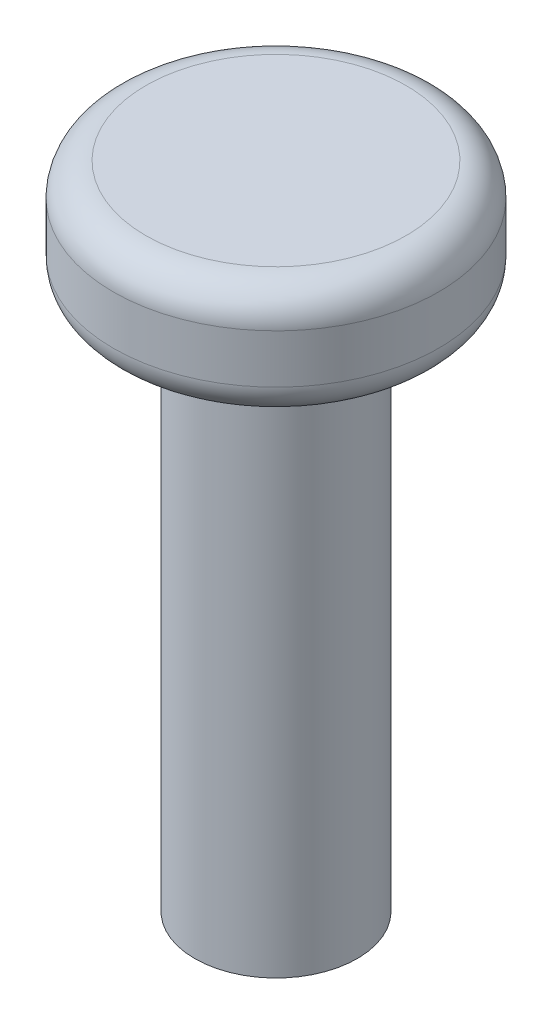
SolidWorks part; units mm, degrees
ref_plane "Front Plane" through (0, 0, 0) normal (0, 0, 1) x (1, 0, 0)
ref_plane "Top Plane" through (0, 0, 0) normal (0, 1, 0) x (1, 0, 0)
ref_plane "Right Plane" through (0, 0, 0) normal (1, 0, 0) x (0, 0, -1)
sketch "Sketch2" plane through (0, 0, 0) normal (0, 1, 0) x (1, 0, 0)
  line L1 (-1, 0.625) -> (1, 0.625)
  line L2 (-1, 0.625) -> (-1, -0.625)
  line L3 (-1, -0.625) -> (1, -0.625)
  line L4 (1, 0.625) -> (1, -0.625)
  line L5 (-1, 0.625) -> (1, -0.625) construction
  line L6 (-1, -0.625) -> (1, 0.625) construction
  circle A0 centre (0, 0) radius 2.5
  dimension "D1" = 5
  dimension "D2" = 1.25
  dimension "D3" = 2
extrude "Boss-Extrude1" add sketch "Sketch2" along normal mid plane 20
fillet "Fillet1" radius 1 1 edges at (0, 10, 2.5)
sketch "Sketch3" plane through (0, 10, 0) normal (0, 1, 0) x (1, 0, 0)
  line L0 (1, -0.625) -> (1, 0.625) construction
  line L1 (-1, -0.625) -> (1, -0.625) construction
  line L2 (-1, 0.625) -> (-1, -0.625) construction
  line L3 (1, 0.625) -> (-1, 0.625) construction
  line L4 (1, -0.625) -> (1, 0.625)
  line L5 (-1, -0.625) -> (1, -0.625)
  line L6 (-1, 0.625) -> (-1, -0.625)
  line L7 (1, 0.625) -> (-1, 0.625)
extrude "Boss-Extrude5" add sketch "Sketch3" against normal blind 16
sketch "Sketch4" plane through (0, 10, 0) normal (0, 1, 0) x (1, 0, 0)
  circle A0 centre (0, 0) radius 5
  point P3 (0, 0)
  dimension "D1" = 10
extrude "Thumb Stick" add sketch "Sketch4" against normal blind 3.5
fillet "Fillet2" radius 1 1 edges at (0, 6.5, 5)
fillet "Fillet3" radius 1 1 edges at (0, 10, 5)
